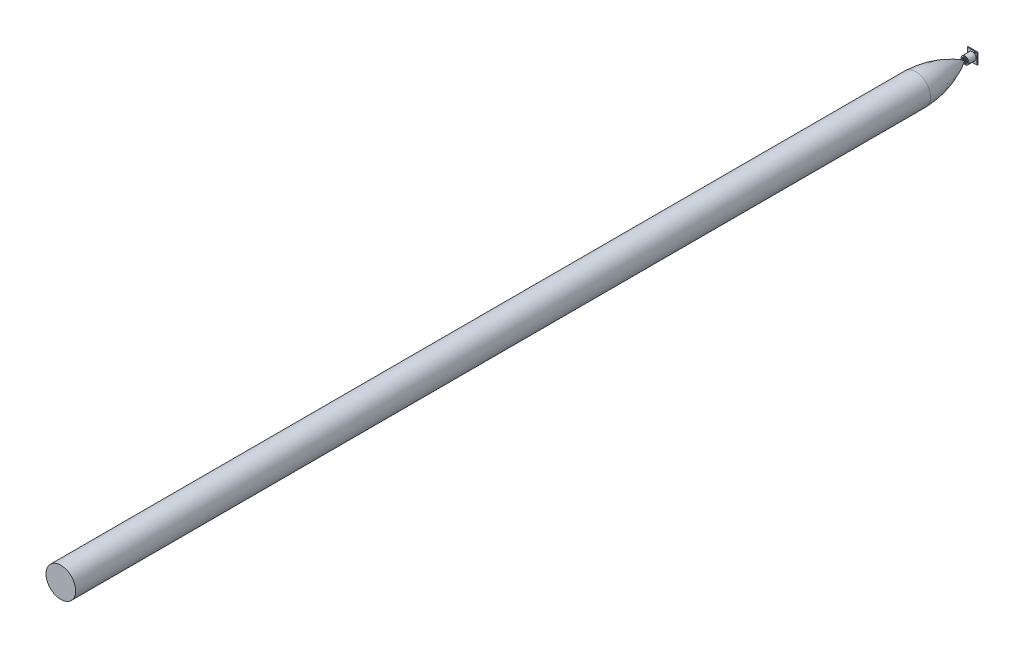
SolidWorks part; units mm, degrees
ref_plane "Front Plane" through (0, 0, 0) normal (0, 0, 1) x (1, 0, 0)
ref_plane "Top Plane" through (0, 0, 0) normal (0, 1, 0) x (1, 0, 0)
ref_plane "Right Plane" through (0, 0, 0) normal (1, 0, 0) x (0, 0, -1)
sketch "Sketch1" plane through (0, 0, 0) normal (0, 0, 1) x (1, 0, 0)
  line L1 (-9.95, -11.05) -> (9.95, -11.05)
  line L2 (-9.95, -11.05) -> (-9.95, 11.05)
  line L3 (-9.95, 11.05) -> (9.95, 11.05)
  line L4 (9.95, -11.05) -> (9.95, 11.05)
  line L5 (-9.95, -11.05) -> (9.95, 11.05) construction
  line L6 (-9.95, 11.05) -> (9.95, -11.05) construction
  point P0 (0, 0)
  dimension "D1" = 19.9
  dimension "D2" = 22.1
extrude "Extrude1" add sketch "Sketch1" along normal blind 1.5875
sketch "Sketch2" plane through (0, 0, 1.5875) normal (0, 0, 1) x (1, 0, 0)
  circle A0 centre (0, 0) radius 7.747
  dimension "D1" = 15.494
extrude "Extrude2" add sketch "Sketch2" along normal blind 14.7955 separate body
sketch "Sketch3" plane through (0, 0, 16.383) normal (0, 0, 1) x (1, 0, 0)
  line L0 (0, 1.905) -> (0, 7.747) construction
  line L1 (1.6498, -0.9525) -> (6.7091, -3.8735) construction
  line L2 (-1.6498, -0.9525) -> (-6.7091, -3.8735) construction
  line L3 (0.508, 1.836) -> (0.508, 3.1341)
  line L4 (-1.844, -0.4781) -> (-2.9682, -1.1271)
  line L5 (1.336, -1.3579) -> (2.4602, -2.007)
  line L6 (-0.508, 1.836) -> (-0.508, 3.1341)
  line L7 (-1.336, -1.3579) -> (-2.4602, -2.007)
  line L8 (1.844, -0.4781) -> (2.9682, -1.1271)
  line L9 (0, 0) -> (6.0492, 3.4925) construction
  line L10 (0.508, -4.4159) -> (0.508, -5.6924)
  line L11 (-0.508, -6.9665) -> (-0.508, -6.985)
  line L12 (0.508, -6.9665) -> (0.508, -6.985)
  line L13 (6.2872, 3.0433) -> (6.3032, 3.0526)
  line L14 (-0.508, -4.4159) -> (-0.508, -5.6924)
  line L15 (5.7792, 3.9232) -> (5.7952, 3.9324)
  line L16 (-6.2872, 3.0433) -> (-6.3032, 3.0526)
  line L19 (-4.0783, 1.768) -> (-5.1837, 2.4062)
  line L20 (-3.5703, 2.6479) -> (-4.6757, 3.2861)
  line L23 (3.5703, 2.6479) -> (4.6757, 3.2861)
  line L24 (4.0783, 1.768) -> (5.1837, 2.4062)
  line L27 (-5.7792, 3.9232) -> (-5.7952, 3.9324)
  circle A0 centre (0, 0) radius 0.635
  arc A1 (-0.508, 1.836) -> (-1.844, -0.4781) centre (0, 0) ccw
  arc A2 (-0.508, 3.1341) -> (-2.9682, -1.1271) centre (0, 0) ccw
  arc A3 (3.5703, 2.6479) -> (-3.5703, 2.6479) centre (0, 0) ccw
  arc A4 (0.508, -5.6924) -> (5.1837, 2.4062) centre (0, 0) ccw
  circle A5 centre (0, 0) radius 6.985
  circle A6 centre (0, 0) radius 7.747 construction
  circle A7 centre (0, 0) radius 1.905 construction
  arc A8 (-1.336, -1.3579) -> (1.336, -1.3579) centre (0, 0) ccw
  arc A9 (1.844, -0.4781) -> (0.508, 1.836) centre (0, 0) ccw
  circle A11 centre (0, 0) radius 3.175 construction
  arc A12 (-2.4602, -2.007) -> (2.4602, -2.007) centre (0, 0) ccw
  arc A13 (2.9682, -1.1271) -> (0.508, 3.1341) centre (0, 0) ccw
  circle A14 centre (0, 0) radius 4.445 construction
  arc A15 (-4.0783, 1.768) -> (-0.508, -4.4159) centre (0, 0) ccw
  arc A16 (0.508, -4.4159) -> (4.0783, 1.768) centre (0, 0) ccw
  circle A17 centre (0, 0) radius 5.715 construction
  arc A18 (4.6757, 3.2861) -> (-4.6757, 3.2861) centre (0, 0) ccw
  arc A19 (-5.1837, 2.4062) -> (-0.508, -5.6924) centre (0, 0) ccw
  dimension "D6" = 1.27
  dimension "D7" = 60
  dimension "D1" = 1.27
  dimension "D2" = 1.27
  dimension "D3" = 1.27
  dimension "D4" = 1.27
  dimension "D5" = 1.27
extrude "Extrude3" cut sketch "Sketch3" against normal blind 2.0955 contours L23 A18 L20 A3 | L19 A19 L14 A15 | L6 A2 L4 A1 | L7 A12 L5 A8 | A0 | L8 A13 L3 A9 | A16 L10 A4 L24
sketch "Sketch4" plane through (0, 0, 0) normal (0, 1, 0) x (1, 0, 0)
  line L0 (0, -16.383) -> (0, -397.383) construction
  line L1 (-7.747, -16.383) -> (7.747, -16.383) construction
  line L2 (0, -16.383) -> (276.8127, -397.383)
  line L3 (276.8127, -397.383) -> (0, -397.383)
  line L4 (0, -16.383) -> (0, -397.383)
  dimension "D1" = 36
  dimension "D2" = 381
revolve "Revolve1" [suppressed] add sketch "Sketch4" angle 360 about L0
sketch "Sketch5" plane through (0, 0, 1.5875) normal (0, 0, 1) x (1, 0, 0)
  line L0 (-9.95, 11.05) -> (-9.95, -11.05) construction
  line L1 (-9.95, -11.05) -> (9.95, -11.05) construction
  circle A0 centre (5.19, 8.49) radius 1.55
  circle A1 centre (-7.41, -8.51) radius 1.55
  dimension "D1" = 3.1
  dimension "D2" = 12.6
  dimension "D3" = 2.54
  dimension "D4" = 17
  dimension "D5" = 2.54
extrude "Cut-Extrude1" cut sketch "Sketch5" against normal through all
sketch "Sketch6" plane through (0, 0, 1.5875) normal (0, 0, 1) x (1, 0, 0)
  line L0 (-9.95, 11.05) -> (-9.95, -11.05) construction
  line L1 (-9.95, -11.05) -> (9.95, -11.05) construction
  circle A0 centre (8.75, 5.89) radius 0.5
  circle A1 centre (8.75, 3.35) radius 0.5
  circle A2 centre (8.75, 0.81) radius 0.5
  circle A3 centre (8.75, -1.73) radius 0.5
  circle A4 centre (8.75, -4.27) radius 0.5
  circle A5 centre (8.75, -6.81) radius 0.5
  circle A6 centre (8.75, -9.35) radius 0.5
  dimension "D2" = 1
  dimension "D5" = 2.54
  dimension "D1" = 18.7
  dimension "D4" = 1.7
  dimension "D3" = 7
extrude "Cut-Extrude2" cut sketch "Sketch6" against normal through all
sketch "Sketch7" plane through (0, 0, 0) normal (1, 0, 0) x (0, 0, -1)
  line L0 (-16.383, 0) -> (-1845.183, 0) construction
  line L2 (-16.383, 7.747) -> (-16.383, -7.747) construction
  line L3 (0, -11.05) -> (0, 11.05) construction
  line L4 (-115.9501, 30) -> (-1845.183, 30)
  line L5 (-16.383, 30) -> (-1845.183, 30) construction
  line L6 (-1845.183, 0) -> (-1845.183, 30)
  line L7 (-16.383, 0) -> (-1845.183, 0)
  spline S0 degree 2 poles (-16.383, 0) (-62.195, 28.1358) (-115.9501, 30) knots 0 0 0 1 1 1
  dimension "D1" = 1828.8
  dimension "D2" = 30
  dimension "D3" = 99.5671
  dimension "D4" = 47.4361
  dimension "D5" = 21.4586
revolve "Revolve2" add sketch "Sketch7" angle 360 about L7
